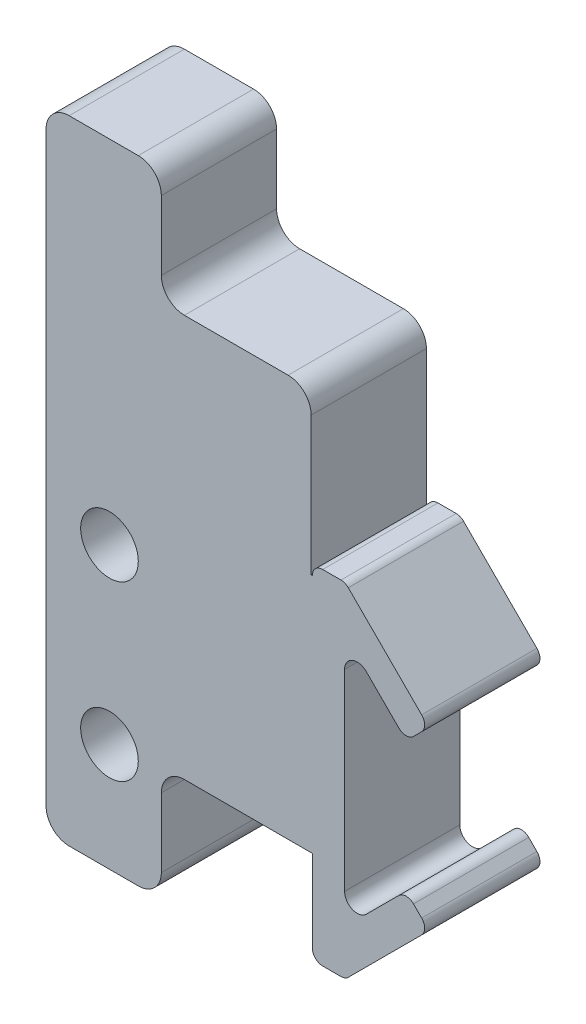
SolidWorks part; units mm, degrees
ref_plane "Plan de face" through (0, 0, 0) normal (0, 0, 1) x (1, 0, 0)
ref_plane "Plan de dessus" through (0, 0, 0) normal (0, 1, 0) x (1, 0, 0)
ref_plane "Plan de droite" through (0, 0, 0) normal (1, 0, 0) x (0, 0, -1)
sketch "Esquisse1" plane through (0, 0, 0) normal (0, 0, 1) x (1, 0, 0)
  line L0 (3.2929, 14.7071) -> (9.6569, 8.3431)
  line L1 (0, 0) -> (3, 0)
  line L2 (0, -14) -> (0, 14)
  line L3 (1, 15) -> (2.5858, 15)
  line L4 (3, -8.3431) -> (3, 8.3431)
  line L5 (10.364, 7.636) -> (3, 15)
  line L6 (9.6569, 6.9289) -> (8.9497, 6.2218)
  line L7 (3, 15) -> (2.9365, 14.9365)
  line L8 (7.5355, 6.2218) -> (4.7071, 9.0503)
  line L9 (7.5355, -6.2218) -> (4.7071, -9.0503)
  line L10 (9.6569, -6.9289) -> (8.9497, -6.2218)
  line L11 (3.2929, -14.7071) -> (9.6569, -8.3431)
  line L12 (1, -15) -> (2.5858, -15)
  line L13 (3.2222, -14.6364) -> (9.5861, -8.2724)
  line L14 (9.5861, -6.9996) -> (8.879, -6.2925)
  line L15 (7.6062, -6.2925) -> (4.7778, -9.121)
  line L16 (2.9, -8.3431) -> (2.9, 8.3431)
  line L17 (7.6062, 6.2925) -> (4.7778, 9.121)
  line L18 (9.5861, 6.9996) -> (8.879, 6.2925)
  line L19 (3.2222, 14.6364) -> (9.5861, 8.2724)
  line L20 (1, 14.9) -> (2.5858, 14.9)
  line L21 (0.1, -14) -> (0.1, 14)
  line L22 (1, -14.9) -> (2.5858, -14.9)
  line L23 (-17.5, 28) -> (-17.5, -6.8817)
  line L24 (0, -6.8817) -> (-23, -6.8817)
  line L25 (0, -6.8817) -> (0, 28)
  line L26 (0, 28) -> (-23, 28)
  line L27 (-23, -6.8817) -> (-23, 28)
  line L28 (0, -6.8817) -> (0.1, -6.8817)
  line L29 (-23, 28) -> (-13, 28)
  line L30 (-23, 28) -> (-23, 38)
  line L31 (-23, 38) -> (-13, 38)
  line L32 (-13, 28) -> (-13, 38)
  line L33 (-23, -6.8817) -> (-13, -6.8817)
  line L34 (-23, -6.8817) -> (-23, -16.8817)
  line L35 (-23, -16.8817) -> (-13, -16.8817)
  line L36 (-13, -6.8817) -> (-13, -16.8817)
  line L37 (0, 14) -> (0.1, 14)
  arc A0 (3, 8.3431) -> (4.7071, 9.0503) centre (4, 8.3431) cw
  arc A1 (8.9497, 6.2218) -> (7.5355, 6.2218) centre (8.2426, 6.9289) cw
  arc A2 (9.6569, 8.3431) -> (9.6569, 6.9289) centre (8.9497, 7.636) cw
  arc A3 (3.2929, 14.7071) -> (2.5858, 15) centre (2.5858, 14) ccw
  arc A4 (1, 15) -> (0, 14) centre (1, 14) ccw
  arc A5 (3, -8.3431) -> (4.7071, -9.0503) centre (4, -8.3431) ccw
  arc A6 (8.9497, -6.2218) -> (7.5355, -6.2218) centre (8.2426, -6.9289) ccw
  arc A7 (9.6569, -8.3431) -> (9.6569, -6.9289) centre (8.9497, -7.636) ccw
  arc A8 (3.2929, -14.7071) -> (2.5858, -15) centre (2.5858, -14) cw
  arc A9 (1, -15) -> (0, -14) centre (1, -14) cw
  arc A10 (9.5861, -8.2724) -> (9.5861, -6.9996) centre (8.9497, -7.636) ccw
  arc A11 (8.879, -6.2925) -> (7.6062, -6.2925) centre (8.2426, -6.9289) ccw
  arc A12 (2.9, -8.3431) -> (4.7778, -9.121) centre (4, -8.3431) ccw
  arc A13 (2.9, 8.3431) -> (4.7778, 9.121) centre (4, 8.3431) cw
  arc A14 (8.879, 6.2925) -> (7.6062, 6.2925) centre (8.2426, 6.9289) cw
  arc A15 (9.5861, 8.2724) -> (9.5861, 6.9996) centre (8.9497, 7.636) cw
  arc A16 (3.2222, 14.6364) -> (2.5858, 14.9) centre (2.5858, 14) ccw
  arc A17 (1, 14.9) -> (0.1, 14) centre (1, 14) ccw
  arc A18 (1, -14.9) -> (0.1, -14) centre (1, -14) cw
  arc A19 (3.2222, -14.6364) -> (2.5858, -14.9) centre (2.5858, -14) cw
  circle A20 centre (-17.5, 7.5) radius 2.5
  circle A21 centre (-17.5, -7.5) radius 2.5
  point P13 (8.2426, 5.5147)
  point P22 (0, 15)
  dimension "D2" = 1
  dimension "D3" = 1
  dimension "D6" = 1
  dimension "D7" = 1
  dimension "D8" = 1
  dimension "D17" = 5
  dimension "D18" = 5
  dimension "D1" = 15
  dimension "D4" = 3
  dimension "D5" = 45
  dimension "D9" = 9
  dimension "D10" = 4
  dimension "D11" = 3
  dimension "D13" = 23
  dimension "D14" = 8.1183
  dimension "D15" = 13
  dimension "D16" = 17.5
  dimension "D19" = 7.5
  dimension "D20" = 7.5
  dimension "D21" = 10
  dimension "D22" = 10
  dimension "D23" = 10
  dimension "D24" = 10
  dimension "D12" = 0.1
extrude "Boss.-Extru.1" add sketch "Esquisse1" along normal blind 10 contours A19 L13 A10 L14 A11 L15 A12 L16 L1 L21 A18 L22 | L20 A17 L21 L1 L16 A13 L17 A14 L18 A15 L19 A16 | L2 L28 L21 L1 | A21 L23 A20 L26 L27 L24 | L36 L24 L34 L35 | L26 L32 L31 L30 | L37 L2 L1 L21 | A21 L23 L24 L2 L25 L26 A20
fillet "Congé1" radius 2 7 edges at (-13, -6.8817, 5) (-23, -16.8817, 5) (-13, -16.8817, 5) (0, 28, 5) (-13, 28, 5) (-13, 38, 5) (-23, 38, 5)
